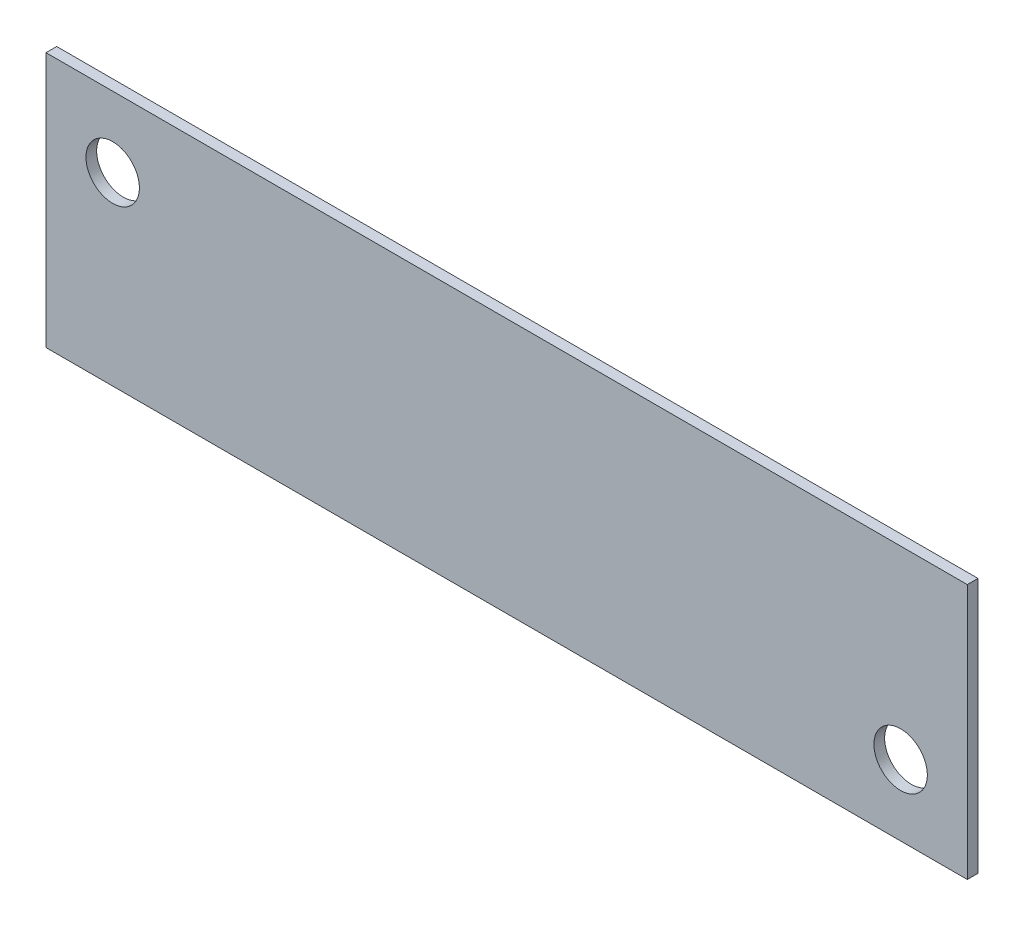
SolidWorks part; units mm, degrees
material "PVC Rigid"
ref_plane "Front" through (0, 0, 0) normal (0, 0, 1) x (1, 0, 0)
ref_plane "Top" through (0, 0, 0) normal (0, 1, 0) x (1, 0, 0)
ref_plane "Right" through (0, 0, 0) normal (1, 0, 0) x (0, 0, -1)
sketch "Sketch1" plane through (0, 0, 0) normal (0, 0, 1) x (1, 0, 0)
  line L1 (-26.15, -3.175) -> (260.15, -3.175) construction
  line L2 (-26.15, -3.175) -> (-26.15, 72.675) construction
  line L3 (-26.15, 72.675) -> (260.15, 72.675) construction
  line L4 (260.15, -3.175) -> (260.15, 72.675) construction
  line L5 (-19.8, 72.675) -> (253.8, 72.675)
  line L6 (-19.8, 72.675) -> (-19.8, -3.175)
  line L7 (-19.8, -3.175) -> (253.8, -3.175)
  line L8 (253.8, 72.675) -> (253.8, -3.175)
  line L10 (260.15, -3.175) -> (-26.15, -3.175) construction
  point P10 (117, 72.675)
  dimension "D1" = 6.35
extrude "Boss-Extrude1" add sketch "Sketch1" along normal blind 3.175
sketch "Sketch2" plane through (0, 0, 3.175) normal (0, 0, 1) x (1, 0, 0)
  circle A0 centre (234, 17.75) radius 6.75 construction
  circle A1 centre (0, 51.75) radius 6.75 construction
  circle A2 centre (234, 17.75) radius 6.75 construction
  circle A3 centre (0, 51.75) radius 6.75 construction
  circle A4 centre (0, 51.75) radius 7.9375
  circle A5 centre (234, 17.75) radius 7.9375
  dimension "D1" = 15.875
extrude "Cut-Extrude1" cut sketch "Sketch2" against normal up to surface (3.175 mm away) up to face at (117, 34.75, 0)
sketch "Sketch3" plane through (0, 0, 3.175) normal (0, 0, 1) x (1, 0, 0)
  circle A0 centre (234, 51.75) radius 6.75 construction
  circle A1 centre (0, 17.75) radius 6.75 construction
  circle A2 centre (234, 51.75) radius 6.75 construction
  circle A3 centre (0, 17.75) radius 6.75 construction
  circle A4 centre (0, 17.75) radius 7.9375
  circle A5 centre (234, 51.75) radius 7.9375
  dimension "D1" = 15.875
extrude "Cut-Extrude2" [suppressed] cut sketch "Sketch3" against normal up to surface (4.7625 mm away)
equation "\"D1@Sketch1\"=\"front and back thickenss@FS2-EN-ACC-A-0002-V1, BATTERY MODULES SEGMENT-1.Assembly\""
